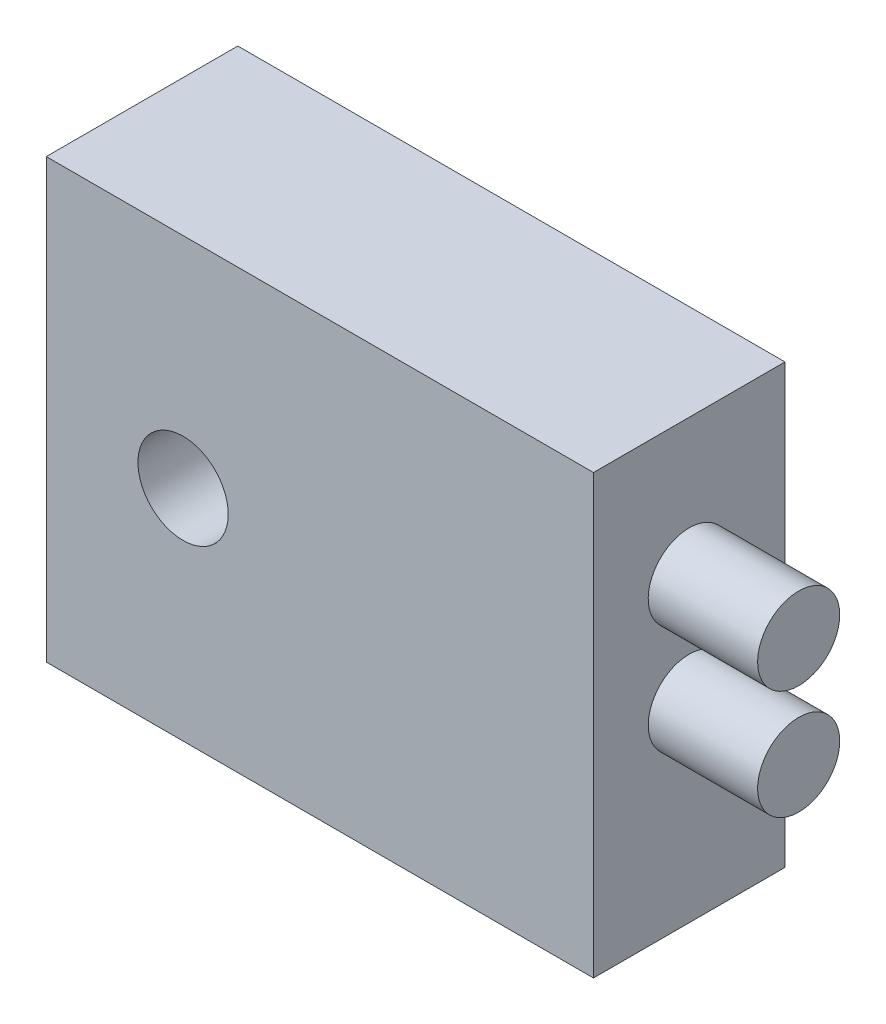
SolidWorks part; units mm, degrees
ref_plane "Front Plane" through (0, 0, 0) normal (0, 0, 1) x (1, 0, 0)
ref_plane "Top Plane" through (0, 0, 0) normal (0, 1, 0) x (1, 0, 0)
ref_plane "Right Plane" through (0, 0, 0) normal (1, 0, 0) x (0, 0, -1)
sketch "Sketch1" plane through (0, 0, 0) normal (0, 0, 1) x (1, 0, 0)
  line L1 (0, 0) -> (20, 0)
  line L2 (0, 0) -> (0, 16)
  line L3 (0, 16) -> (20, 16)
  line L4 (20, 0) -> (20, 16)
  circle A0 centre (5, 8) radius 1.65
  dimension "D3" = 3.3
  dimension "D5" = 8
  dimension "D1" = 20
  dimension "D2" = 16
  dimension "D4" = 5
extrude "Boss-Extrude1" add sketch "Sketch1" along normal blind 7
sketch "Sketch2" plane through (20, 0, 0) normal (1, 0, 0) x (0, 0, -1)
  line L0 (-7, 0) -> (0, 0) construction
  circle A0 centre (-3.5, 7) radius 1.5
  circle A1 centre (-3.5, 11) radius 1.5
  point P5 (-3.5, 0)
  dimension "D1" = 3
  dimension "D2" = 7
  dimension "D3" = 3
  dimension "D4" = 4
extrude "Boss-Extrude2" add sketch "Sketch2" along normal blind 4
